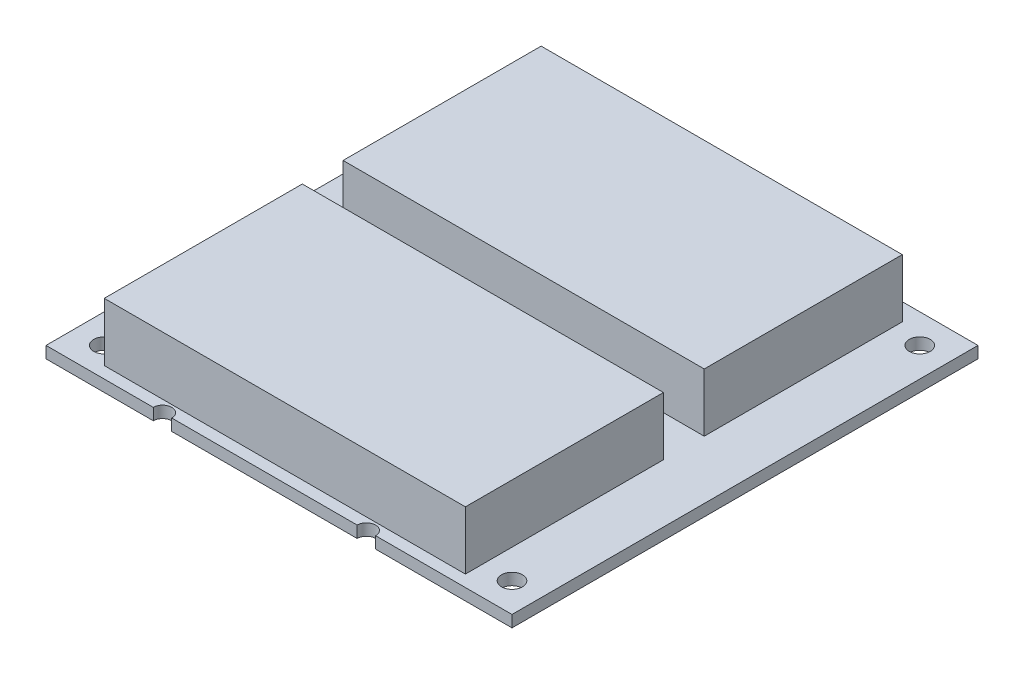
SolidWorks part; units mm, degrees
ref_plane "Front Plane" through (0, 0, 0) normal (0, 0, 1) x (1, 0, 0)
ref_plane "Top Plane" through (0, 0, 0) normal (0, 1, 0) x (1, 0, 0)
ref_plane "Right Plane" through (0, 0, 0) normal (1, 0, 0) x (0, 0, -1)
sketch "Sketch1" plane through (0, 0, 0) normal (0, 1, 0) x (1, 0, 0)
  line L1 (0, 0) -> (80, 0)
  line L2 (0, 0) -> (0, 80)
  line L3 (0, 80) -> (80, 80)
  line L4 (80, 0) -> (80, 80)
  dimension "D1" = 80
  dimension "D2" = 80
extrude "PCB" add sketch "Sketch1" along normal blind 2
sketch "Sketch3" plane through (0, 2, 0) normal (0, 1, 0) x (1, 0, 0)
  line L0 (0, 80) -> (0, 0) construction
  line L3 (8, 36) -> (70, 36)
  line L4 (8, 36) -> (8, 2)
  line L5 (8, 2) -> (70, 2)
  line L6 (70, 36) -> (70, 2)
  line L7 (0, 0) -> (80, 0) construction
  dimension "D1" = 34
  dimension "D2" = 62
  dimension "D3" = 8
  dimension "D4" = 2
extrude "Battery Stack" add sketch "Sketch3" along normal blind 10
pattern_linear "LPattern3" count 2 spacing 41 along (0, 0, -1) of "Battery Stack"
sketch "Sketch4" plane through (0, 2, 0) normal (0, 1, 0) x (1, 0, 0)
  line L0 (0, 80) -> (0, 0) construction
  line L1 (80, 80) -> (0, 80) construction
  line L3 (80, 0) -> (80, 80) construction
  line L4 (0, 0) -> (80, 0) construction
  circle A0 centre (5, 75) radius 1.8
  circle A1 centre (75, 75) radius 1.8
  circle A2 centre (75, 5) radius 1.8
  circle A3 centre (5, 5) radius 1.8
  dimension "D3" = 3.6
  dimension "D4" = 5
  dimension "D6" = 3.6
  dimension "D9" = 3.6
  dimension "D12" = 3.6
  dimension "D1" = 5
  dimension "D2" = 5
  dimension "D5" = 5
  dimension "D7" = 5
  dimension "D8" = 5
  dimension "D10" = 5
  dimension "D11" = 5
extrude "Attachment holes" cut sketch "Sketch4" against normal through all
sketch "Sketch6" plane through (0, 2, 0) normal (0, 1, 0) x (1, 0, 0)
  line L0 (0, 0) -> (80, 0) construction
  line L1 (0, 80) -> (0, 0) construction
  circle A0 centre (20, 0) radius 1.5875
  dimension "D1" = 3.175
  dimension "D2" = 0
  dimension "D3" = 20
extrude "Battery Cable Tie Holes" cut sketch "Sketch6" against normal through all
pattern_linear "LPattern2" count 2 spacing 35 along (1, 0, 0) count 3 spacing 40 along (0, 0, -1) of "Battery Cable Tie Holes"
